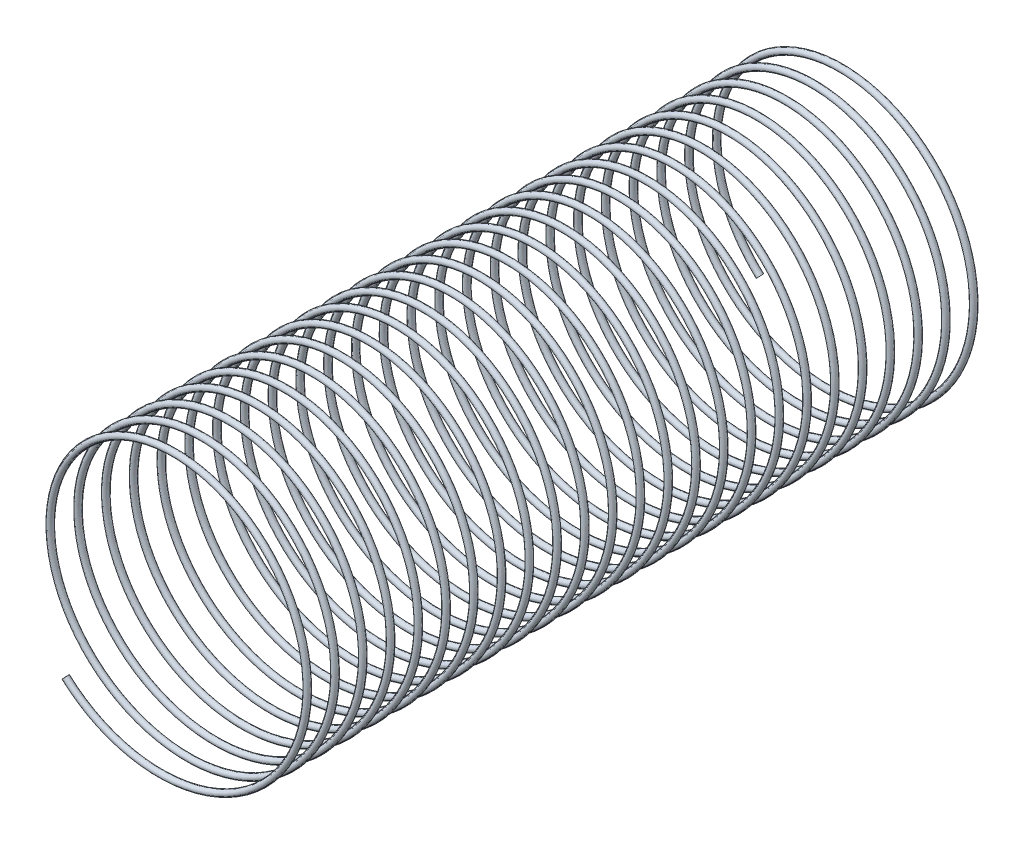
SolidWorks part; units mm, degrees
ref_plane "Front Plane" through (0, 0, 0) normal (0, 0, 1) x (1, 0, 0)
ref_plane "Top Plane" through (0, 0, 0) normal (0, 1, 0) x (1, 0, 0)
ref_plane "Right Plane" through (0, 0, 0) normal (1, 0, 0) x (0, 0, -1)
sketch "Sketch8" plane through (0, 0, 0) normal (0, 0, 1) x (1, 0, 0)
  circle A0 centre (0, 0) radius 9.906
  dimension "D1" = 19.812
curve "Helix/Spiral2" pitch 2.032 height 50.8 turns 25
sweep "Sweep2" add path "Helix/Spiral2" circular profile diameter 0.4547 parameters "D3"=0.4547
